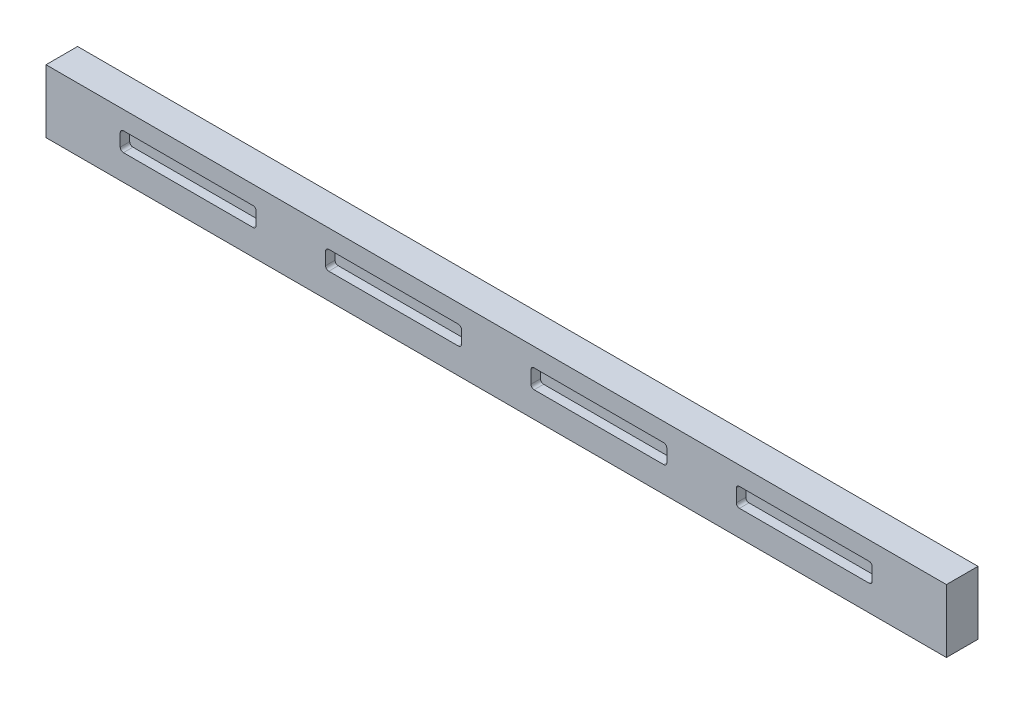
SolidWorks part; units mm, degrees
ref_plane "Front Plane" through (0, 0, 0) normal (0, 0, 1) x (1, 0, 0)
ref_plane "Top Plane" through (0, 0, 0) normal (0, 1, 0) x (1, 0, 0)
ref_plane "Right Plane" through (0, 0, 0) normal (1, 0, 0) x (0, 0, -1)
sketch "Sketch1" plane through (0, 0, 27.5) normal (0, 0, 1) x (1, 0, 0)
  line L1 (-142.5, 23) -> (142.5, 23)
  line L2 (-142.5, 23) -> (-142.5, 3)
  line L3 (-142.5, 3) -> (142.5, 3)
  line L4 (142.5, 23) -> (142.5, 3)
extrude "Boss-Extrude1" add sketch "Sketch1" along normal blind 10
sketch "Sketch5" plane through (0, 0, 37.5) normal (0, 0, 1) x (1, 0, 0)
  line L0 (142.5, 23) -> (-142.5, 23) construction
  line L1 (-119, 11.15) -> (-76, 11.15)
  line L2 (-119, 11.15) -> (-119, 17.15)
  line L3 (-119, 17.15) -> (-76, 17.15)
  line L4 (-76, 11.15) -> (-76, 17.15)
  line L5 (-119, 11.15) -> (-76, 17.15) construction
  line L6 (-119, 17.15) -> (-76, 11.15) construction
  line L7 (-54, 11.15) -> (-11, 11.15)
  line L8 (-54, 11.15) -> (-54, 17.15)
  line L9 (-54, 17.15) -> (-11, 17.15)
  line L10 (-11, 11.15) -> (-11, 17.15)
  line L11 (-54, 11.15) -> (-11, 17.15) construction
  line L12 (-54, 17.15) -> (-11, 11.15) construction
  line L13 (11, 11.15) -> (54, 11.15)
  line L14 (11, 11.15) -> (11, 17.15)
  line L15 (11, 17.15) -> (54, 17.15)
  line L16 (54, 11.15) -> (54, 17.15)
  line L17 (11, 11.15) -> (54, 17.15) construction
  line L18 (11, 17.15) -> (54, 11.15) construction
  line L19 (76, 11.15) -> (119, 11.15)
  line L20 (76, 11.15) -> (76, 17.15)
  line L21 (76, 17.15) -> (119, 17.15)
  line L22 (119, 11.15) -> (119, 17.15)
  line L23 (76, 11.15) -> (119, 17.15) construction
  line L24 (76, 17.15) -> (119, 11.15) construction
  line L25 (142.5, 3) -> (142.5, 23) construction
  line L26 (-142.5, 23) -> (-142.5, 3) construction
  point P0 (-97.5, 14.15)
  point P5 (-32.5, 14.15)
  point P10 (32.5, 14.15)
  point P15 (97.5, 14.15)
  point P22 (142.5, 13)
  dimension "D1" = 43
  dimension "D2" = 6
  dimension "D3" = 43
  dimension "D4" = 6
  dimension "D5" = 43
  dimension "D6" = 6
  dimension "D7" = 43
  dimension "D8" = 6
  dimension "D9" = 5.85
  dimension "D10" = 5.85
  dimension "D11" = 5.85
  dimension "D12" = 5.85
  dimension "D13" = 23.5
  dimension "D14" = 23.5
  dimension "D15" = 22
  dimension "D16" = 22
extrude "Cut-Extrude1" cut sketch "Sketch5" against normal blind 3
fillet "Fillet1" radius 1 16 edges at (119, 17.15, 36) (119, 11.15, 36) (76, 17.15, 36) (76, 11.15, 36) (54, 17.15, 36) (54, 11.15, 36) (11, 17.15, 36) (11, 11.15, 36) (-11, 17.15, 36) (-11, 11.15, 36) (-54, 17.15, 36) (-54, 11.15, 36) (-76, 11.15, 36) (-76, 17.15, 36) (-119, 11.15, 36) (-119, 17.15, 36)
